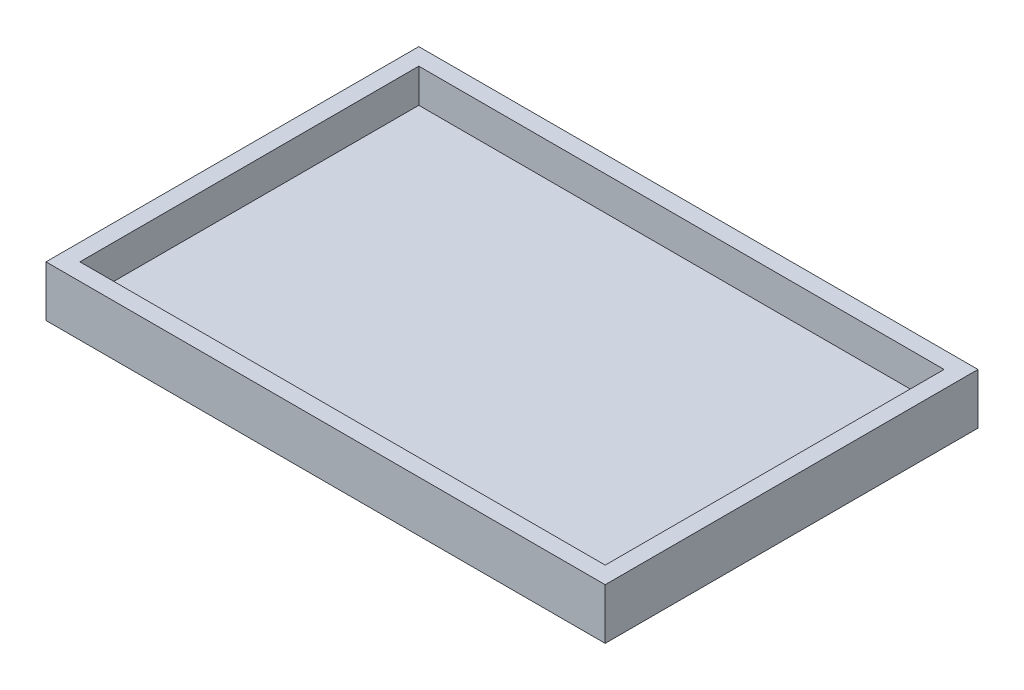
SolidWorks part; units mm, degrees
ref_plane "前视基准面" through (0, 0, 0) normal (0, 0, 1) x (1, 0, 0)
ref_plane "上视基准面" through (0, 0, 0) normal (0, 1, 0) x (1, 0, 0)
ref_plane "右视基准面" through (0, 0, 0) normal (1, 0, 0) x (0, 0, -1)
sketch "草图1" plane through (0, 0, 0) normal (0, 1, 0) x (1, 0, 0)
  line L0 (0, 0) -> (66, 0)
  line L1 (66, 0) -> (66, 44)
  line L2 (66, 44) -> (0, 44)
  line L3 (0, 44) -> (0, 0)
extrude "凸台-拉伸1" add sketch "草图1" along normal blind 6
sketch "草图2" plane through (0, 6, 0) normal (0, 1, 0) x (1, 0, 0)
  line L1 (2, 2) -> (64, 2)
  line L2 (2, 2) -> (2, 42)
  line L3 (2, 42) -> (64, 42)
  line L4 (64, 2) -> (64, 42)
extrude "切除-拉伸1" cut sketch "草图2" against normal blind 4
